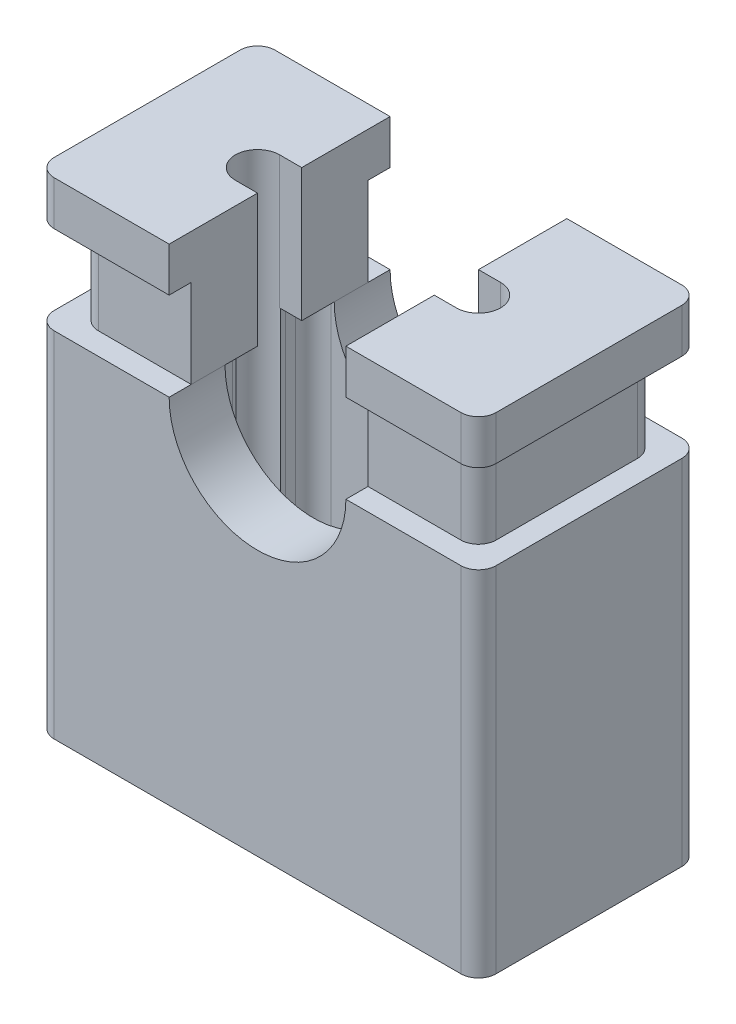
SolidWorks part; units mm, degrees
ref_plane "Ön Düzlem" through (0, 0, 0) normal (0, 0, 1) x (1, 0, 0)
ref_plane "Üst Düzlem" through (0, 0, 0) normal (0, 1, 0) x (1, 0, 0)
ref_plane "Sağ Düzlem" through (0, 0, 0) normal (1, 0, 0) x (0, 0, -1)
sketch "Çizim1" plane through (0, 0, 0) normal (0, 1, 0) x (1, 0, 0)
  line L0 (-2.5, 0) -> (-1.2359, 0) construction
  line L1 (-2.3, 1.25) -> (2.3, 1.25)
  line L2 (-2.5, 1.05) -> (-2.5, -1.05)
  line L3 (-2.3, -1.25) -> (2.3, -1.25)
  line L4 (2.5, 1.05) -> (2.5, -1.05)
  line L5 (-2.5, 1.25) -> (-1.2359, 0.6179) construction
  line L6 (-2.5, -1.25) -> (-1.2359, -0.6179) construction
  line L7 (2.5, 0) -> (1.5, 0) construction
  line L8 (1.2359, -0.3) -> (1.2359, -0.4179)
  line L9 (0, 1.25) -> (0, 0.6179) construction
  line L12 (-1.2359, -0.3) -> (-1.2359, -0.4179)
  line L13 (-1.0359, 0.6179) -> (1.0359, 0.6179)
  line L14 (-1.2359, 0.4179) -> (-1.2359, 0.3)
  line L15 (-1.0359, -0.6179) -> (1.0359, -0.6179)
  line L16 (1.2359, 0.4179) -> (1.2359, 0.3)
  line L19 (1.5, 0) -> (2.5, 0) construction
  line L22 (0, -0.6179) -> (0, -1.25) construction
  line L23 (1.2359, -0.6179) -> (2.5, -1.25) construction
  line L26 (1.2359, 0.6179) -> (2.5, 1.25) construction
  line L27 (0, 0.6179) -> (0, 1.25) construction
  arc A0 (2.3, -1.25) -> (2.5, -1.05) centre (2.3, -1.05) ccw
  arc A1 (-2.5, -1.05) -> (-2.3, -1.25) centre (-2.3, -1.05) ccw
  arc A2 (2.3, 1.25) -> (2.5, 1.05) centre (2.3, 1.05) cw
  arc A3 (-2.3, 1.25) -> (-2.5, 1.05) centre (-2.3, 1.05) ccw
  arc A4 (-1.2422, 0.2499) -> (-1.2422, -0.2499) centre (-1.25, 0) ccw
  arc A5 (1.2422, -0.2499) -> (1.2422, 0.2499) centre (1.25, 0) ccw
  arc A6 (1.2422, -0.2499) -> (1.2359, -0.3) centre (1.4359, -0.3) ccw
  arc A7 (1.2422, 0.2499) -> (1.2359, 0.3) centre (1.4359, 0.3) cw
  arc A8 (-1.2422, -0.2499) -> (-1.2359, -0.3) centre (-1.4359, -0.3) cw
  arc A9 (-1.2422, 0.2499) -> (-1.2359, 0.3) centre (-1.4359, 0.3) ccw
  arc A10 (-1.2359, -0.4179) -> (-1.0359, -0.6179) centre (-1.0359, -0.4179) ccw
  arc A11 (1.0359, -0.6179) -> (1.2359, -0.4179) centre (1.0359, -0.4179) ccw
  arc A12 (1.0359, 0.6179) -> (1.2359, 0.4179) centre (1.0359, 0.4179) cw
  arc A13 (-1.0359, 0.6179) -> (-1.2359, 0.4179) centre (-1.0359, 0.4179) ccw
  point P0 (0, 0)
  point P37 (1.2359, -0.1)
  point P47 (-1.2359, -0.1)
  dimension "D3" = 0.2
  dimension "D4" = 0.5
  dimension "D5" = 0.5
  dimension "D7" = 0.2
  dimension "D8" = 0.2
  dimension "D10" = 1.25
  dimension "D1" = 5
  dimension "D2" = 2.5
  dimension "D9" = 1.25
extrude "Yükseklik-Ekstrüzyon1" add sketch "Çizim1" along normal blind 4
sketch "Çizim3" plane through (0, 4, 0) normal (0, 1, 0) x (1, 0, 0)
  line L0 (-1.25, 0.25) -> (1.25, 0.25)
  line L1 (-2.05, -1) -> (2.05, -1)
  line L2 (-2.25, -0.8) -> (-2.25, 0.8)
  line L3 (-2.05, 1) -> (2.05, 1)
  line L4 (2.25, -0.8) -> (2.25, 0.8)
  line L5 (-2.25, -1) -> (2.25, 1) construction
  line L6 (-2.25, 1) -> (2.25, -1) construction
  line L7 (-1.25, -0.25) -> (1.25, -0.25)
  arc A0 (2.05, 1) -> (2.25, 0.8) centre (2.05, 0.8) cw
  arc A1 (2.05, -1) -> (2.25, -0.8) centre (2.05, -0.8) ccw
  arc A2 (-2.05, -1) -> (-2.25, -0.8) centre (-2.05, -0.8) cw
  arc A3 (-2.25, 0.8) -> (-2.05, 1) centre (-2.05, 0.8) cw
  arc A4 (-1.25, 0.25) -> (-1.25, -0.25) centre (-1.25, 0) ccw
  arc A5 (1.25, -0.25) -> (1.25, 0.25) centre (1.25, 0) ccw
  point P0 (0, 0)
  dimension "D3" = 0.2
  dimension "D1" = 4.5
  dimension "D2" = 2
extrude "Yükseklik-Ekstrüzyon2" add sketch "Çizim3" along normal blind 1
sketch "Çizim4" plane through (0, 5, 0) normal (0, 1, 0) x (1, 0, 0)
  line L0 (1.25, 0.25) -> (-1.25, 0.25)
  line L1 (-2.3, 1.25) -> (2.3, 1.25)
  line L2 (-2.5, 1.05) -> (-2.5, -1.05)
  line L3 (-2.3, -1.25) -> (2.3, -1.25)
  line L4 (2.5, 1.05) -> (2.5, -1.05)
  line L5 (-2.5, 1.25) -> (2.5, -1.25) construction
  line L6 (-2.5, -1.25) -> (2.5, 1.25) construction
  arc A0 (2.3, -1.25) -> (2.5, -1.05) centre (2.3, -1.05) ccw
  arc A1 (2.3, 1.25) -> (2.5, 1.05) centre (2.3, 1.05) cw
  arc A2 (-2.5, -1.05) -> (-2.3, -1.25) centre (-2.3, -1.05) ccw
  arc A3 (-2.3, 1.25) -> (-2.5, 1.05) centre (-2.3, 1.05) ccw
  point P0 (0, 0)
  arc M9 (2.25, 0.8) -> (2.05, 1) centre (2.05, 0.8) ccw
  line M10 (2.05, 1) -> (-2.05, 1)
  arc M11 (-2.05, 1) -> (-2.25, 0.8) centre (-2.05, 0.8) ccw
  line M12 (-2.25, 0.8) -> (-2.25, -0.8)
  arc M13 (-2.25, -0.8) -> (-2.05, -1) centre (-2.05, -0.8) ccw
  line M14 (-2.05, -1) -> (2.05, -1)
  arc M15 (2.05, -1) -> (2.25, -0.8) centre (2.05, -0.8) ccw
  line M16 (2.25, -0.8) -> (2.25, 0.8)
  arc M17 (-1.25, -0.25) -> (-1.25, 0.25) centre (-1.25, 0) cw
  line M18 (-1.25, 0.25) -> (1.25, 0.25)
  arc M19 (1.25, 0.25) -> (1.25, -0.25) centre (1.25, 0) cw
  line M20 (1.25, -0.25) -> (-1.25, -0.25)
  dimension "D1" = 0.2
extrude "Yükseklik-Ekstrüzyon3" add sketch "Çizim4" along normal blind 0.5 contours L1 A3 L2 A2 L3 A0 L4 A1 M9 M16 M15 M14 M13 M12 M11 M10 | M16 M9 M10 M11 M12 M13 M14 M15 M20 M17 M18 M19
sketch "Çizim5" plane through (0, 0, -1.25) normal (0, 0, -1) x (-1, 0, 0)
  line L0 (0, 0) -> (0, 4) construction
  line L1 (-2.3, 0) -> (2.3, 0) construction
  line L2 (-2.05, 4) -> (2.05, 4) construction
  line L3 (0, 4) -> (0, 5.5) construction
  line L4 (2.3, 5.5) -> (-2.3, 5.5) construction
  line L5 (-1, 4) -> (-1, 5.5)
  line L6 (-1, 5.5) -> (1, 5.5)
  line L7 (1, 5.5) -> (1, 4)
  arc A0 (-1, 4) -> (1, 4) centre (0, 4) ccw
  dimension "D1" = 2
extrude "Kes-Ekstrüzyon1" cut sketch "Çizim5" against normal through all
